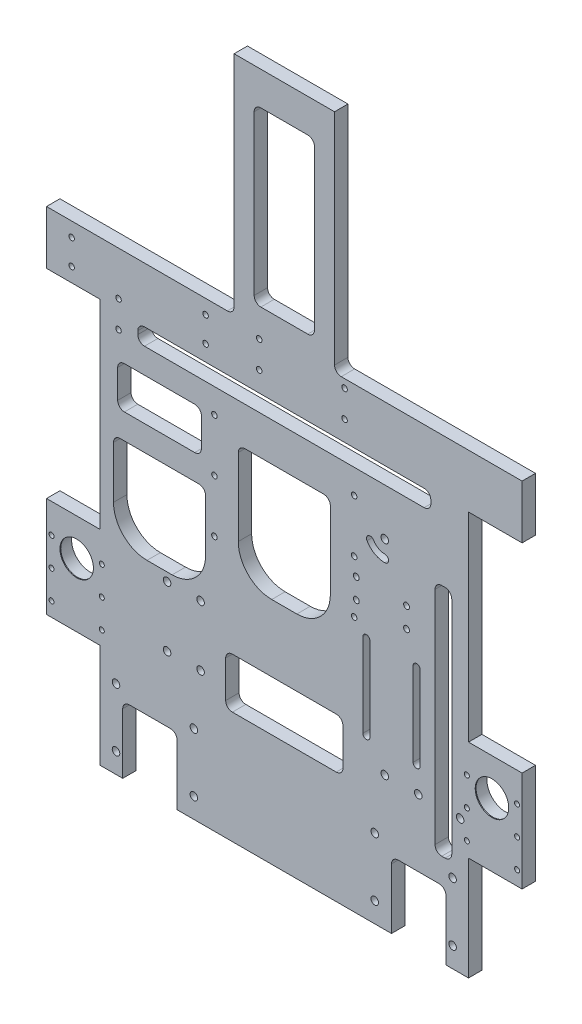
SolidWorks part; units mm, degrees
ref_plane "Front" through (0, 0, 0) normal (0, 0, 1) x (1, 0, 0)
ref_plane "Top" through (0, 0, 0) normal (0, 1, 0) x (1, 0, 0)
ref_plane "Right" through (0, 0, 0) normal (1, 0, 0) x (0, 0, -1)
sketch "Esquisse1" plane through (0, 0, 0) normal (0, 0, 1) x (1, 0, 0)
  line L1 (0, 0) -> (220, 0)
  line L2 (0, 0) -> (0, 285)
  line L3 (0, 285) -> (220, 285)
  line L4 (220, 0) -> (220, 285)
  dimension "D1" = 220
  dimension "D2" = 285
extrude "Boss.-Extru.1" add sketch "Esquisse1" along normal blind 8
sketch "Esquisse2" plane through (0, 0, 0) normal (0, -1, 0) x (1, 0, 0)
  line L0 (0, 4) -> (220, 4) construction
  line L1 (0, 8) -> (0, 0) construction
  line L2 (220, 8) -> (220, 0) construction
  line L3 (110, 4) -> (110, 28.0559) construction
  circle A0 centre (110, 4) radius 2
  circle A1 centre (213, 4) radius 2
  circle A2 centre (7, 4) radius 2
  dimension "D1" = 4
  dimension "D2" = 103
extrude "Enlèv. mat.-Extru.1" cut sketch "Esquisse2" against normal blind 8
sketch "Esquisse3" plane through (0, 0, 8) normal (0, 0, 1) x (1, 0, 0)
  line L0 (110, 0) -> (110, 285) construction
  line L1 (0, 0) -> (220, 0) construction
  line L2 (220, 285) -> (0, 285) construction
  line L3 (82.5, 207) -> (137.5, 207)
  line L4 (137.5, 207) -> (137.5, 137)
  line L5 (137.5, 137) -> (82.5, 137)
  line L6 (82.5, 207) -> (82.5, 137)
  line L8 (8, 175) -> (63, 175)
  line L9 (8, 175) -> (8, 120)
  line L10 (8, 120) -> (63, 120)
  line L11 (63, 175) -> (63, 120)
  line L12 (200, 55) -> (210, 55)
  line L13 (200, 55) -> (200, 195)
  line L14 (200, 195) -> (210, 195)
  line L15 (210, 55) -> (210, 195)
  point P11 (110, 137)
  point P12 (110, 207)
  dimension "D1" = 70
  dimension "D2" = 55
  dimension "D3" = 137
  dimension "D4" = 55
  dimension "D5" = 47
  dimension "D6" = 55
  dimension "D7" = 120
  dimension "D8" = 140
  dimension "D9" = 55
  dimension "D10" = 90
  dimension "D11" = 10
extrude "Enlèv. mat.-Extru.2" cut sketch "Esquisse3" against normal through all both and the other way through all
sketch "Esquisse5" plane through (0, 0, 8) normal (0, 0, 1) x (1, 0, 0)
  line L0 (110, 230) -> (110, 0) construction
  line L1 (22.5, 240) -> (197.5, 240)
  line L2 (22.5, 240) -> (22.5, 230)
  line L3 (22.5, 230) -> (197.5, 230)
  line L4 (197.5, 240) -> (197.5, 230)
  line L5 (0, 0) -> (220, 0) construction
  dimension "D1" = 175
  dimension "D2" = 10
  dimension "D3" = 230
extrude "Enlèv. mat.-Extru.3" cut sketch "Esquisse5" against normal through all both and the other way through all
sketch "Esquisse6" plane through (0, 0, 8) normal (0, 0, 1) x (1, 0, 0)
  line L0 (170, 80) -> (190, 80) construction
  line L1 (0, 0) -> (220, 0) construction
  line L2 (137.5, 137) -> (82.5, 137) construction
  line L3 (215, 80) -> (190, 80) construction
  line L4 (168, 191.6799) -> (168, 168) construction
  line L5 (186.4274, 168) -> (149.5726, 168) construction
  line L6 (0, 285) -> (0, 0) construction
  circle A0 centre (190, 80) radius 2.25
  circle A1 centre (170, 80) radius 2.25
  circle A2 centre (215, 80) radius 2.25
  circle A3 centre (153, 174) radius 1.75
  circle A4 centre (183, 174) radius 1.75
  circle A5 centre (183, 162) radius 1.75
  circle A6 centre (153, 162) radius 1.75
  point P8 (110, 137)
  dimension "D1" = 4.5
  dimension "D3" = 80
  dimension "D6" = 30
  dimension "D7" = 12
  dimension "D8" = 3.5
  dimension "D2" = 20
  dimension "D4" = 60
  dimension "D5" = 25
  dimension "D9" = 168
  dimension "D10" = 168
extrude "Enlèv. mat.-Extru.4" cut sketch "Esquisse6" against normal through all both and the other way through all
sketch "Esquisse7" plane through (0, 0, 8) normal (0, 0, 1) x (1, 0, 0)
  line L0 (110, 0) -> (110, 285) construction
  line L1 (0, 0) -> (220, 0) construction
  line L2 (220, 285) -> (0, 285) construction
  line L3 (68.285, 184) -> (68.285, 215.4) construction
  line L4 (68.285, 184) -> (110, 184) construction
  line L5 (151.715, 184) -> (151.715, 215.4) construction
  line L6 (95, 268) -> (120.5, 268) construction
  line L7 (120.5, 268) -> (120.5, 260) construction
  line L8 (120.5, 260) -> (137.9818, 260) construction
  line L9 (95, 252) -> (120.5, 252) construction
  line L10 (22.5, 240) -> (197.5, 240) construction
  circle A0 centre (68.285, 215.4) radius 1.65
  circle A1 centre (68.285, 184) radius 1.65
  circle A2 centre (68.285, 152.6) radius 1.65
  circle A3 centre (151.715, 152.6) radius 1.65
  circle A4 centre (151.715, 184) radius 1.65
  circle A5 centre (151.715, 215.4) radius 1.65
  circle A6 centre (95, 268) radius 1.65
  circle A7 centre (146, 268) radius 1.65
  circle A8 centre (146, 252) radius 1.65
  circle A9 centre (95, 252) radius 1.65
  dimension "D1" = 31.4
  dimension "D2" = 3.3
  dimension "D5" = 16
  dimension "D6" = 51
  dimension "D9" = 3.3
  dimension "D7" = 15
  dimension "D3" = 83.43
  dimension "D4" = 184
  dimension "D8" = 20
extrude "Enlèv. mat.-Extru.5" cut sketch "Esquisse7" against normal through all both and the other way through all
sketch "Esquisse8" plane through (0, 0, 8) normal (0, 0, 1) x (1, 0, 0)
  line L0 (110, 0) -> (110, 285) construction
  line L1 (0, 0) -> (220, 0) construction
  line L2 (220, 285) -> (0, 285) construction
  line L3 (174, 0) -> (174, 40)
  line L4 (13.5, 0) -> (46, 0)
  line L5 (13.5, 0) -> (13.5, 40)
  line L6 (13.5, 40) -> (46, 40)
  line L7 (46, 0) -> (46, 40)
  line L8 (206.5, 40) -> (174, 40)
  line L9 (206.5, 0) -> (206.5, 40)
  line L10 (206.5, 0) -> (174, 0)
  dimension "D1" = 128
  dimension "D2" = 32.5
  dimension "D3" = 40
extrude "Enlèv. mat.-Extru.6" cut sketch "Esquisse8" against normal through all both and the other way through all
fillet "Congé1" radius 20 4 edges at (137.5, 137, 4) (82.5, 137, 4) (63, 120, 4) (8, 120, 4)
sketch "Esquisse9" plane through (0, 0, 8) normal (0, 0, 1) x (1, 0, 0)
  line L0 (189, 145) -> (189, 95) construction
  line L1 (191.1, 145) -> (191.1, 95)
  line L2 (186.9, 145) -> (186.9, 95)
  line L3 (189, 120) -> (159, 120) construction
  line L4 (174, 120) -> (174, 121.5076) construction
  line L5 (159, 95) -> (159, 145) construction
  line L6 (156.9, 95) -> (156.9, 145)
  line L7 (161.1, 95) -> (161.1, 145)
  line L9 (210, 55) -> (200, 55) construction
  line L10 (200, 55) -> (200, 195) construction
  arc A0 (191.1, 145) -> (186.9, 145) centre (189, 145) ccw
  arc A1 (186.9, 95) -> (191.1, 95) centre (189, 95) ccw
  arc A2 (156.9, 95) -> (161.1, 95) centre (159, 95) ccw
  arc A3 (161.1, 145) -> (156.9, 145) centre (159, 145) ccw
  point P2 (189, 120)
  point P13 (159, 120)
  dimension "D1" = 4.2
  dimension "D2" = 30
  dimension "D3" = 11
  dimension "D4" = 40
  dimension "D5" = 50
extrude "Enlèv. mat.-Extru.7" cut sketch "Esquisse9" against normal through all both and the other way through all
sketch "Esquisse10" plane through (0, 0, 8) normal (0, 0, 1) x (1, 0, 0)
  line L0 (9.5, 0) -> (9.5, 52.9697) construction
  line L1 (0, 0) -> (13.5, 0) construction
  line L2 (0, 285) -> (0, 0) construction
  line L3 (110, 0) -> (110, 48.9194) construction
  line L4 (46, 0) -> (174, 0) construction
  line L5 (32.75, 0) -> (32.75, 52.9697) construction
  circle A0 centre (9.5, 12) radius 2.25
  circle A1 centre (9.5, 47) radius 2.25
  circle A2 centre (210.5, 47) radius 2.25
  circle A3 centre (210.5, 12) radius 2.25
  circle A4 centre (56, 47) radius 2.25
  circle A5 centre (56, 12) radius 2.25
  circle A6 centre (164, 12) radius 2.25
  circle A7 centre (164, 47) radius 2.25
  dimension "D2" = 4.5
  dimension "D3" = 35
  dimension "D4" = 12
  dimension "D5" = 46.5
  dimension "D1" = 9.5
extrude "Enlèv. mat.-Extru.8" cut sketch "Esquisse10" against normal through all both and the other way through all
sketch "Esquisse11" plane through (0, 0, 8) normal (0, 0, 1) x (1, 0, 0)
  line L0 (110, 67) -> (110, 0) construction
  line L1 (75, 97) -> (145, 97)
  line L2 (75, 97) -> (75, 67)
  line L3 (75, 67) -> (145, 67)
  line L4 (145, 97) -> (145, 67)
  line L5 (46, 0) -> (174, 0) construction
  dimension "D1" = 70
  dimension "D2" = 30
  dimension "D3" = 67
extrude "Enlèv. mat.-Extru.9" cut sketch "Esquisse11" against normal through all both and the other way through all
sketch "Esquisse12" plane through (0, 0, 8) normal (0, 0, 1) x (1, 0, 0)
  line L0 (220, 0) -> (220, 285) construction
  line L1 (46, 0) -> (174, 0) construction
  line L2 (170, 202) -> (161.3397, 197) construction
  line L3 (170, 192) -> (170, 202) construction
  circle A0 centre (170, 202) radius 2.25
  arc A1 (161.3397, 197) -> (170, 192) centre (170, 202) ccw construction
  arc A2 (159.3912, 195.875) -> (170, 189.75) centre (170, 202) ccw
  arc A3 (163.2883, 198.125) -> (170, 194.25) centre (170, 202) ccw
  arc A4 (163.2883, 198.125) -> (159.3912, 195.875) centre (161.3397, 197) ccw
  arc A5 (170, 189.75) -> (170, 194.25) centre (170, 192) ccw
  point P9 (165, 193.3397)
  dimension "D1" = 4.5
  dimension "D2" = 50
  dimension "D3" = 202
  dimension "D4" = 4.5
  dimension "D5" = 10
  dimension "D6" = 60
extrude "Enlèv. mat.-Extru.10" cut sketch "Esquisse12" against normal through all both and the other way through all
sketch "Esquisse13" plane through (0, 0, 8) normal (0, 0, 1) x (1, 0, 0)
  line L0 (50, 123.132) -> (50, 97) construction
  line L1 (50, 97) -> (30.3926, 97) construction
  line L2 (46, 0) -> (174, 0) construction
  line L3 (0, 285) -> (0, 0) construction
  circle A0 centre (40, 115) radius 2.25
  circle A1 centre (60, 115) radius 2.25
  circle A2 centre (60, 79) radius 2.25
  circle A3 centre (40, 79) radius 2.25
  dimension "D1" = 36
  dimension "D2" = 20
  dimension "D3" = 4.5
  dimension "D4" = 97
  dimension "D5" = 40
extrude "Enlèv. mat.-Extru.11" cut sketch "Esquisse13" against normal through all both and the other way through all
sketch "Esquisse14" plane through (0, 0, 8) normal (0, 0, 1) x (1, 0, 0)
  line L0 (110, 0) -> (110, 159.9943) construction
  line L1 (0, 285) -> (80, 285)
  line L2 (0, 285) -> (0, 273)
  line L3 (0, 273) -> (80, 273)
  line L4 (80, 285) -> (80, 273)
  line L5 (46, 0) -> (174, 0) construction
  line L6 (140, 285) -> (140, 273)
  line L7 (220, 273) -> (140, 273)
  line L8 (220, 285) -> (220, 273)
  line L9 (220, 285) -> (140, 285)
  dimension "D1" = 12
  dimension "D2" = 80
extrude "Enlèv. mat.-Extru.12" cut sketch "Esquisse14" against normal through all both and the other way through all
sketch "Esquisse15" plane through (0, 0, 8) normal (0, 0, 1) x (1, 0, 0)
  line L0 (140, 285) -> (80, 285) construction
  line L1 (80, 285) -> (140, 285)
  line L2 (80, 285) -> (80, 408)
  line L3 (80, 408) -> (140, 408)
  line L4 (140, 285) -> (140, 408)
  line L5 (110, 408) -> (110, 0) construction
  line L6 (46, 0) -> (174, 0) construction
  dimension "D1" = 60
  dimension "D2" = 123
extrude "Boss.-Extru.2" add sketch "Esquisse15" against normal up to vertex (8 mm away) up to point (13.5, 0, 0)
sketch "Esquisse16" plane through (0, 0, 8) normal (0, 0, 1) x (1, 0, 0)
  line L0 (110, 388) -> (110, 408) construction
  line L1 (92, 285) -> (128, 285)
  line L2 (92, 285) -> (92, 388)
  line L3 (92, 388) -> (128, 388)
  line L4 (128, 285) -> (128, 388)
  line L5 (140, 408) -> (80, 408) construction
  line L6 (140, 273) -> (140, 408) construction
  line L7 (80, 273) -> (0, 273) construction
  dimension "D1" = 12
  dimension "D2" = 20
  dimension "D3" = 12
extrude "Enlèv. mat.-Extru.13" cut sketch "Esquisse16" against normal through all both and the other way through all
sketch "Esquisse17" plane through (0, 0, 8) normal (0, 0, 1) x (1, 0, 0)
  line L0 (110, 0) -> (110, -39.2027) construction
  line L1 (220, 273) -> (252, 273)
  line L2 (220, 273) -> (220, 241)
  line L3 (220, 241) -> (252, 241)
  line L4 (252, 273) -> (252, 241)
  line L5 (46, 0) -> (174, 0) construction
  line L6 (-32, 273) -> (-32, 241)
  line L7 (0, 241) -> (-32, 241)
  line L8 (0, 273) -> (0, 241)
  line L9 (0, 273) -> (-32, 273)
  line L10 (0, 273) -> (0, 0) construction
  line L11 (0, 62) -> (-32, 62)
  line L12 (0, 62) -> (0, 122)
  line L13 (0, 122) -> (-32, 122)
  line L14 (-32, 62) -> (-32, 122)
  line L15 (252, 62) -> (252, 122)
  line L16 (220, 122) -> (252, 122)
  line L17 (220, 62) -> (220, 122)
  line L18 (220, 62) -> (252, 62)
  dimension "D1" = 32
  dimension "D2" = 32
  dimension "D3" = 60
  dimension "D4" = 62
extrude "Boss.-Extru.3" add sketch "Esquisse17" against normal up to vertex (8 mm away)
sketch "Esquisse18" plane through (0, 0, 8) normal (0, 0, 1) x (1, 0, 0)
  line L0 (35.5, 190) -> (35.5, 175) construction
  line L1 (10.5, 190) -> (60.5, 190)
  line L2 (10.5, 190) -> (10.5, 215)
  line L3 (10.5, 215) -> (60.5, 215)
  line L4 (60.5, 190) -> (60.5, 215)
  line L5 (8, 175) -> (63, 175) construction
  dimension "D1" = 25
  dimension "D2" = 50
  dimension "D3" = 15
extrude "Enlèv. mat.-Extru.14" cut sketch "Esquisse18" against normal through all both and the other way through all
fillet "Congé2" radius 4 30 edges at (137.5, 207, 4) (82.5, 207, 4) (197.5, 230, 4) (197.5, 240, 4) (22.5, 240, 4) (22.5, 230, 4) (63, 175, 4) (8, 175, 4) (200, 195, 4) (210, 195, 4) (210, 55, 4) (200, 55, 4) (206.5, 40, 4) (174, 40, 4) (46, 40, 4) (13.5, 40, 4) (75, 67, 4) (145, 67, 4) (145, 97, 4) (75, 97, 4) (92, 388, 4) (128, 388, 4) (128, 285, 4) (92, 285, 4) (140, 273, 4) (80, 273, 4) (10.5, 215, 4) (60.5, 215, 4) (60.5, 190, 4) (10.5, 190, 4)
sketch "Esquisse19" plane through (0, 0, 8) normal (0, 0, 1) x (1, 0, 0)
  line L0 (-32, 257) -> (54.3473, 257) construction
  line L1 (-32, 273) -> (-32, 241) construction
  line L2 (23, 257) -> (23, 269.1) construction
  line L3 (11, 230.8) -> (11, 246.8) construction
  circle A0 centre (-17, 264.5) radius 1.65
  circle A1 centre (-17, 249.5) radius 1.65
  circle A2 centre (63, 249.5) radius 1.65
  circle A3 centre (63, 264.5) radius 1.65
  circle A4 centre (11, 246.8) radius 1.65
  circle A5 centre (11, 230.8) radius 1.65
  dimension "D2" = 80
  dimension "D3" = 3.3
  dimension "D5" = 28
  dimension "D6" = 16
  dimension "D7" = 10.2
  dimension "D1" = 15
  dimension "D4" = 55
extrude "Enlèv. mat.-Extru.15" cut sketch "Esquisse19" against normal through all both and the other way through all
sketch "Esquisse20" plane through (0, 0, 0) normal (0, 0, 1) x (1, 0, 0)
  line L0 (-32, 100) -> (-14, 100) construction
  line L2 (110, 0) -> (110, 74.504) construction
  line L3 (46, 0) -> (174, 0) construction
  line L4 (252, 100) -> (234, 100) construction
  line L5 (-32, 122) -> (-32, 62) construction
  circle A0 centre (-14, 100) radius 11.025
  circle A1 centre (234, 100) radius 11.025
  dimension "D1" = 22.05
  dimension "D3" = 100
  dimension "D2" = 18
extrude "Enlèv. mat.-Extru.16" cut sketch "Esquisse20" along normal blind 7.5
sketch "Esquisse21" plane through (0, 0, 7.5) normal (0, 0, -1) x (-1, 0, 0)
  line L0 (-110, 0) -> (-110, 78) construction
  line L1 (-46, 0) -> (-174, 0) construction
  circle A0 centre (14, 100) radius 10
  circle A1 centre (-234, 100) radius 10
  dimension "D1" = 20
extrude "Enlèv. mat.-Extru.17" cut sketch "Esquisse21" against normal through all both and the other way through all
sketch "Esquisse22" plane through (0, 0, 8) normal (0, 0, 1) x (1, 0, 0)
  line L0 (-14, 104.5) -> (-14, 70.5) construction
  line L1 (-14, 70.5) -> (-29, 70.5) construction
  line L2 (-14, 87.5) -> (-29, 87.5) construction
  line L3 (-14, 104.5) -> (-14, 110) construction
  line L4 (-29, 70.5) -> (-29, 87.5) construction
  line L5 (-14, 110) -> (-4, 100) construction
  line L6 (-24, 100) -> (-14, 110) construction
  line L7 (-24, 100) -> (-4, 100) construction
  line L8 (110, 0) -> (110, 176.4772) construction
  line L9 (46, 0) -> (174, 0) construction
  line L10 (244, 100) -> (224, 100) construction
  line L11 (244, 100) -> (234, 110) construction
  line L12 (234, 110) -> (224, 100) construction
  line L13 (249, 70.5) -> (249, 87.5) construction
  line L14 (234, 104.5) -> (234, 110) construction
  line L15 (234, 87.5) -> (249, 87.5) construction
  line L16 (234, 70.5) -> (249, 70.5) construction
  line L17 (234, 104.5) -> (234, 70.5) construction
  circle A0 centre (-29, 70.5) radius 1.5
  circle A1 centre (-29, 87.5) radius 1.5
  circle A2 centre (-29, 104.5) radius 1.5
  circle A3 centre (1, 104.5) radius 1.5
  circle A4 centre (1, 87.5) radius 1.5
  circle A5 centre (1, 70.5) radius 1.5
  circle A7 centre (-14, 100) radius 10 construction
  circle A8 centre (219, 70.5) radius 1.5
  circle A9 centre (219, 87.5) radius 1.5
  circle A10 centre (219, 104.5) radius 1.5
  circle A11 centre (249, 104.5) radius 1.5
  circle A12 centre (249, 87.5) radius 1.5
  circle A13 centre (249, 70.5) radius 1.5
  dimension "D1" = 3
  dimension "D2" = 30
  dimension "D3" = 17
  dimension "D4" = 12.5
extrude "Enlèv. mat.-Extru.18" cut sketch "Esquisse22" against normal through all both and the other way through all
